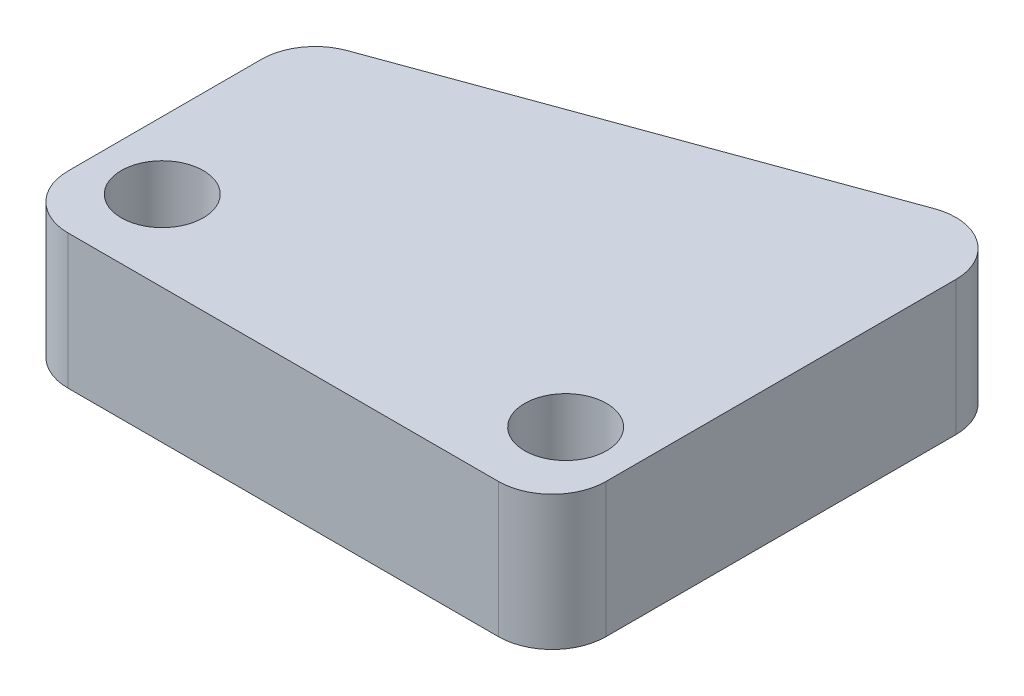
SolidWorks part; units mm, degrees
material "Thornel Mat VMA"
ref_plane "前视基准面" through (0, 0, 0) normal (0, 0, 1) x (1, 0, 0)
ref_plane "上视基准面" through (0, 0, 0) normal (0, 1, 0) x (1, 0, 0)
ref_plane "右视基准面" through (0, 0, 0) normal (1, 0, 0) x (0, 0, -1)
other "Configuration Table"
sketch "草图1" plane through (0, 0, 0) normal (0, 1, 0) x (1, 0, 0)
  line L1 (-10, -10) -> (10, -10)
  line L2 (-10, -10) -> (-10, 10)
  line L3 (-10, 10) -> (10, 10)
  line L4 (10, -10) -> (10, 10)
  line L5 (-10, -10) -> (10, 10) construction
  line L6 (-10, 10) -> (10, -10) construction
  point P0 (0, 0)
  dimension "D1" = 20
  dimension "D2" = 20
extrude "凸台-拉伸1" add sketch "草图1" along normal blind 5
sketch "草图2" plane through (0, 5, 0) normal (0, 1, 0) x (1, 0, 0)
  line L0 (-10, -10) -> (10, -10) construction
  line L1 (-7.5, -7) -> (7.5, -7) construction
  circle A0 centre (-7.5, -7) radius 1.525
  circle A1 centre (7.5, -7) radius 1.525
  dimension "D3" = 3.05
  dimension "D4" = 3.05
  dimension "D1" = 7.5
  dimension "D2" = 15
  dimension "D5" = 3
extrude "切除-拉伸1" cut sketch "草图2" against normal blind 10 contours A0 | A1
sketch "草图3" plane through (0, 5, 0) normal (0, 1, 0) x (1, 0, 0)
  line L2 (-130.9261, -43.4277) -> (29.9243, 15.1171)
  line L3 (3.0757, 88.8829) -> (-157.7747, 30.3382)
  line L4 (-130.9261, -43.4277) -> (29.9243, 15.1171)
  line L5 (3.0757, 88.8829) -> (-157.7747, 30.3382)
  line L8 (10, -10) -> (10, 10)
  line L9 (10, 10) -> (-10, 10)
  line L10 (-10, 10) -> (-10, -10)
  line L11 (-10, -10) -> (10, -10)
  line L12 (10, -10) -> (10, 10)
  line L13 (10, 10) -> (-10, 10)
  line L14 (-10, 10) -> (-10, -10)
  line L15 (-10, -10) -> (10, -10)
  arc A4 (-175.7071, 28.1525) -> (-146.0681, -53.28) centre (-180.8355, -19.8242) ccw
  arc A5 (-130.9261, -43.4277) -> (-146.0681, -53.28) centre (-117.2453, -81.0154) ccw
  arc A6 (29.9243, 15.1171) -> (3.0757, 88.8829) centre (16.5, 52) ccw
  arc A7 (-175.7071, 28.1525) -> (-157.7747, 30.3382) centre (-171.4555, 67.9259) ccw
  arc A8 (-175.7071, 28.1525) -> (-146.0681, -53.28) centre (-180.8355, -19.8242) ccw
  arc A9 (-130.9261, -43.4277) -> (-146.0681, -53.28) centre (-117.2453, -81.0154) ccw
  arc A10 (29.9243, 15.1171) -> (3.0757, 88.8829) centre (16.5, 52) ccw
  arc A11 (-175.7071, 28.1525) -> (-157.7747, 30.3382) centre (-171.4555, 67.9259) ccw
  line M13 (10, -10) -> (10, 10)
  line M14 (10, 10) -> (-10, 10)
  line M15 (-10, 10) -> (-10, -10)
  dimension "D1" = 0
  dimension "D2" = 0
extrude "切除-拉伸2" cut sketch "草图3" against normal through all contours L4 M15 M13 M14
sketch "草图4" plane through (0, 5, 0) normal (0, 1, 0) x (1, 0, 0)
  line L1 (-10, 0.5858) -> (-10, -10) construction
  line L2 (-9.9829, 0.5388) -> (10.0171, 7.8182)
  line L3 (-10, 0.5326) -> (10, 7.812)
  line L4 (10, -10) -> (10, 7.8652) construction
  line L9 (10, -10) -> (10, 7.8652)
  line L10 (10, 7.8652) -> (-10, 0.5858)
  line L11 (-10, 0.5858) -> (-10, -10)
  line L12 (-10, -10) -> (10, -10)
  line L13 (10, -10) -> (10, 7.8652)
  line L14 (10, 7.8652) -> (-10, 0.5858)
  line L15 (-10, 0.5858) -> (-10, -10)
  line L16 (-10, -10) -> (10, -10)
  dimension "D1" = 0.05
  dimension "D2" = 0
fillet "圆角2" radius 2 4 edges at (-10, 2.5, 10) (10, 2.5, 10) (-10, 2.5, -0.5858) (10, 2.5, -7.8652)
